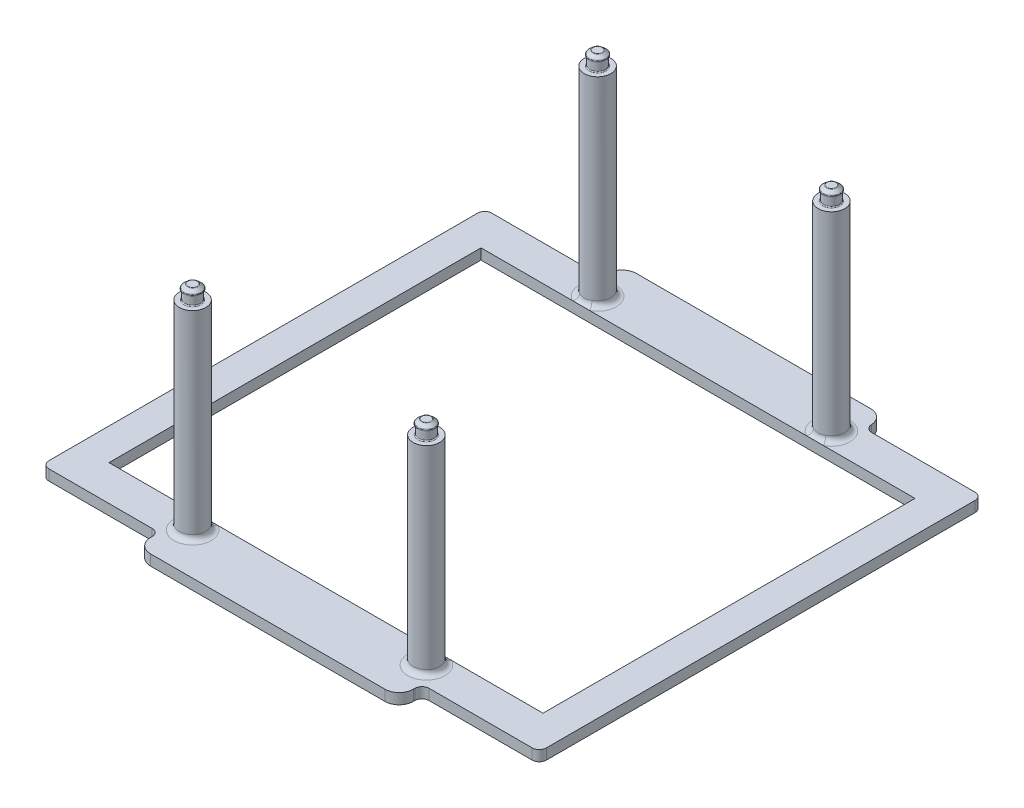
SolidWorks part; units mm, degrees
ref_plane "Front Plane" through (0, 0, 0) normal (0, 0, 1) x (1, 0, 0)
ref_plane "Top Plane" through (0, 0, 0) normal (0, 1, 0) x (1, 0, 0)
ref_plane "Right Plane" through (0, 0, 0) normal (1, 0, 0) x (0, 0, -1)
sketch "Sketch1" plane through (0, 0, 0) normal (0, 1, 0) x (1, 0, 0)
  line L0 (0, 0) -> (0, -52.8) construction
  line L1 (0, 0) -> (0, 52.8) construction
  line L2 (0, 0) -> (-26.4, 45.7261) construction
  line L3 (0, 0) -> (26.4, 45.7261) construction
  line L4 (0, 0) -> (-26.4, -45.7261) construction
  line L5 (0, 0) -> (26.4, -45.7261) construction
  line L6 (0, 50) -> (-29.6654, 54.5367) construction
  line L12 (29.6654, 50) -> (29.6654, 54.5367)
  line L13 (56.1644, -50) -> (29.6654, -50)
  line L14 (56.1644, -50) -> (56.1644, 50)
  line L15 (56.1644, 50) -> (29.6654, 50)
  line L16 (-56.1644, -50) -> (-56.1644, 50)
  line L17 (56.1644, -50) -> (-56.1644, 50) construction
  line L18 (56.1644, 50) -> (-56.1644, -50) construction
  line L19 (29.6654, 54.5367) -> (-29.6654, 54.5367)
  line L20 (-29.6654, 50) -> (-29.6654, 54.5367)
  line L21 (-29.6654, 50) -> (-56.1644, 50)
  line L22 (29.6654, 54.5367) -> (0, 50) construction
  line L24 (29.6654, -55.1514) -> (-29.6654, -55.1514)
  line L25 (29.6654, -55.1514) -> (29.6654, -50)
  line L27 (-29.6654, -55.1514) -> (-29.6654, -50)
  line L28 (29.6654, -55.1514) -> (0, -50) construction
  line L29 (-29.6654, -50) -> (-56.1644, -50)
  line L30 (0, -50) -> (-29.6654, -55.1514) construction
  circle A0 centre (0, 0) radius 52.8 construction
  point P8 (0, 50)
  point P17 (0, -50)
  dimension "D1" = 30
  dimension "D2" = 30
  dimension "D3" = 30
  dimension "D4" = 30
  dimension "D7" = 112.3288
  dimension "D8" = 100
extrude "Boss-Extrude1" add sketch "Sketch1" along normal blind 2.4
ref_plane "Plane1" through (0, 2.4, 0) normal (0, 1, 0) x (1, 0, 0)
sketch "Sketch2" plane through (0, 2.4, 0) normal (0, 1, 0) x (1, 0, 0)
  line L1 (49, 42) -> (-49, 42)
  line L2 (49, 42) -> (49, -42)
  line L3 (49, -42) -> (-49, -42)
  line L4 (-49, 42) -> (-49, -42)
  line L5 (49, 42) -> (-49, -42) construction
  line L6 (49, -42) -> (-49, 42) construction
  point P0 (0, 0)
  dimension "D1" = 84
  dimension "D2" = 98
extrude "Cut-Extrude1" cut sketch "Sketch2" against normal blind 2.4
sketch "Sketch3" plane through (0, 2.4, 0) normal (0, 1, 0) x (1, 0, 0)
  line L0 (0, 0) -> (0, 59.0547) construction
  line L1 (0, 0) -> (0, -60.329) construction
  line L2 (0, 0) -> (-28.291, 49.0014) construction
  line L3 (0, 0) -> (28.291, 49.0014) construction
  line L4 (0, 0) -> (-28.4113, -49.2098) construction
  line L5 (0, 0) -> (28.4113, -49.2098) construction
  circle A0 centre (0, 0) radius 52.8 construction
  circle A1 centre (-26.4, 45.7261) radius 3
  circle A2 centre (26.4, 45.7261) radius 3
  circle A3 centre (-26.4, -45.7261) radius 3
  circle A4 centre (26.4, -45.7261) radius 3
  dimension "D1" = 30
  dimension "D2" = 30
extrude "Boss-Extrude2" add sketch "Sketch3" along normal blind 45
fillet "Fillet1" radius 1.2 4 edges at (-26.4, 2.4, -42.7261) (26.4, 2.4, -42.7261) (26.4, 2.4, 48.7261) (-26.4, 2.4, 48.7261)
fillet "Fillet2" radius 3.2 4 edges at (-29.6654, 1.2, -54.5367) (29.6654, 1.2, -54.5367) (29.6654, 1.2, 55.1514) (-29.6654, 1.2, 55.1514)
fillet "Fillet3" radius 1.6 8 edges at (-56.1644, 1.2, -50) (-29.6654, 1.2, -50) (56.1644, 1.2, -50) (29.6654, 1.2, -50) (29.6654, 1.2, 50) (56.1644, 1.2, 50) (-29.6654, 1.2, 50) (-56.1644, 1.2, 50)
ref_plane "Plane2" through (0, 47.4, 0) normal (0, 1, 0) x (1, 0, 0)
sketch "Sketch4" plane through (0, 47.4, 0) normal (0, 1, 0) x (1, 0, 0)
  circle A0 centre (-26.4, 45.7261) radius 1.75
  circle A1 centre (26.4, 45.7261) radius 1.75
  circle A2 centre (26.4, -45.7261) radius 1.75
  circle A3 centre (-26.4, -45.7261) radius 1.75
extrude "Boss-Extrude3" add sketch "Sketch4" along normal blind 2.14
ref_plane "Plane3" through (0, 49.54, 0) normal (0, 1, 0) x (1, 0, 0)
sketch "Sketch5" plane through (0, 49.54, 0) normal (0, 1, 0) x (1, 0, 0)
  circle A0 centre (-26.4, 45.7261) radius 1.94
  circle A1 centre (-26.4, 45.7261) radius 1.75 construction
  circle A2 centre (26.3924, 45.7261) radius 1.94
  circle A3 centre (26.3924, -45.7473) radius 1.94
  circle A4 centre (-26.4, -45.7261) radius 1.9746
  circle A5 centre (-26.4, -45.7261) radius 1.75 construction
extrude "Boss-Extrude4" add sketch "Sketch5" along normal blind 1
chamfer "Chamfer1" distance 0.75 angle 50 4 edges at (-26.4, 50.54, 47.7007) (26.3924, 50.54, 47.6873) (26.3924, 50.54, -43.7861) (-26.4, 50.54, -43.7861)
fillet "Fillet4" radius 0.2 12 edges at (-26.4, 47.4, 47.4761) (-26.4, 49.79, 47.7007) (-26.4, 50.54, 46.8069) (26.4, 47.4, 47.4761) (26.3924, 49.79, 47.6873) (26.3924, 50.54, 46.7935) (26.4, 47.4, -43.9761) (26.3924, 49.79, -43.7861) (26.3924, 50.54, -44.68) (-26.4, 47.4, -43.9761) (-26.4, 49.79, -43.7861) (-26.4, 50.54, -44.68)
scale "Scale1" bodies to scale 105 scale about centroid uniform scaling yes scale factor 1.15
sketch "Sketch6" plane through (0, 2.4, 0) normal (0, 1, 0) x (1, 0, 0)
  text T0 "<b>Origami Lift </b>\r\n<b>/ Actuator</b>"
